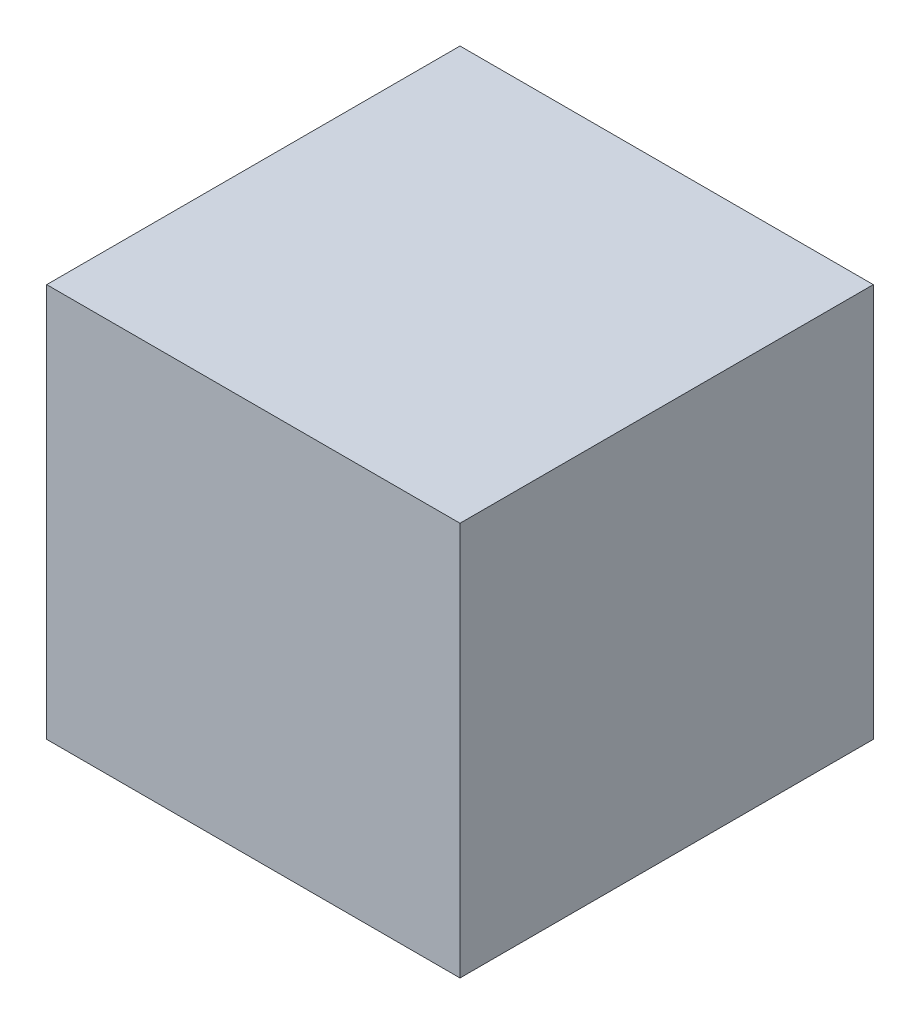
SolidWorks part; units mm, degrees
ref_plane "Front Plane" through (0, 0, 0) normal (0, 0, 1) x (1, 0, 0)
ref_plane "Top Plane" through (0, 0, 0) normal (0, 1, 0) x (1, 0, 0)
ref_plane "Right Plane" through (0, 0, 0) normal (1, 0, 0) x (0, 0, -1)
sketch "Sketch2" plane through (0, 0, 0) normal (0, 1, 0) x (1, 0, 0)
  line L1 (0, 0) -> (42.24, 0)
  line L2 (0, 0) -> (0, 42.24)
  line L3 (0, 42.24) -> (42.24, 42.24)
  line L4 (42.24, 0) -> (42.24, 42.24)
  dimension "D1" = 42.24
extrude "Boss-Extrude1" add sketch "Sketch2" along normal blind 40.25
